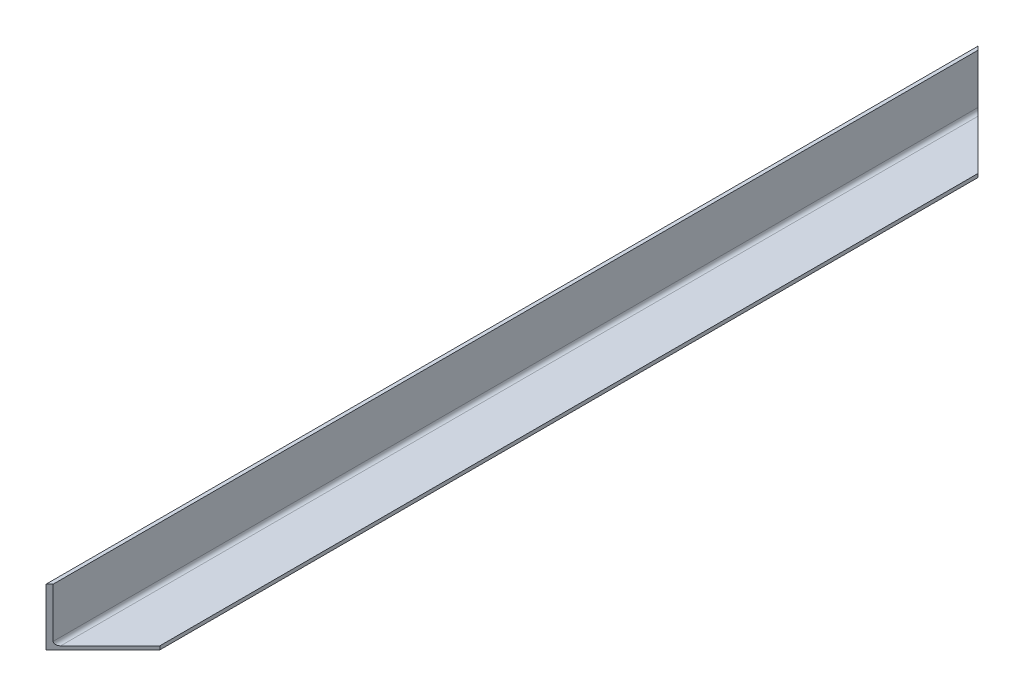
SolidWorks part; units mm, degrees
ref_plane "Front Plane" through (0, 0, 0) normal (0, 0, 1) x (1, 0, 0)
ref_plane "Top Plane" through (0, 0, 0) normal (0, 1, 0) x (1, 0, 0)
ref_plane "Right Plane" through (0, 0, 0) normal (1, 0, 0) x (0, 0, -1)
sketch "Sketch1" plane through (0, 0, 0) normal (0, 0, 1) x (1, 0, 0)
  line L0 (0, -25.4) -> (0, 25.4) construction
  line L1 (25.4, 0) -> (-25.4, 0) construction
  line L2 (-25.4, 25.4) -> (-25.4, -25.4) construction
  line L3 (-25.4, -25.4) -> (25.4, -25.4) construction
  line L4 (25.4, -25.4) -> (25.4, -22.225) construction
  line L5 (25.4, -22.225) -> (-22.225, -22.225) construction
  line L6 (-22.225, -22.225) -> (-22.225, 25.4) construction
  line L7 (-22.225, 25.4) -> (-25.4, 25.4) construction
  line L8 (-22.225, -22.225) -> (-25.4, -22.225) construction
  line L9 (-22.225, -22.225) -> (-22.225, -25.4) construction
  point P4 (0, 0)
  point P8 (0, 0)
  dimension "Wall Thickness" = 3.175
  dimension "Outside Height" = 50.8
  dimension "Outside Width" = 50.8
  dimension "Inside Width" = 47.625
  dimension "Inside Height" = 47.625
sketch "Sketch2" plane through (0, 0, 0) normal (1, 0, 0) x (0, 0, -1)
  line L0 (415.925, 0) -> (-415.925, 0) construction
  line L1 (415.925, -25.4) -> (-415.925, -25.4) construction
  point P0 (-352.425, 0)
  point P4 (0, 0)
  point P5 (352.425, 0)
  point P9 (0, -25.4)
  dimension "Length" = 831.85
  dimension "D1" = 63.5
  dimension "D2" = 63.5
sketch "Sketch4" plane through (0, 0, 0) normal (0, 0, 1) x (1, 0, 0)
  line L0 (-22.225, -22.225) -> (-22.225, 25.4) construction
  line L1 (25.4, -22.225) -> (-22.225, -22.225) construction
  line L2 (25.4, -25.4) -> (25.4, -22.225) construction
  line L3 (-25.4, -25.4) -> (25.4, -25.4) construction
  line L4 (-25.4, 25.4) -> (-25.4, -25.4) construction
  line L5 (-22.225, 25.4) -> (-25.4, 25.4) construction
  line L6 (-22.225, -18.8383) -> (-22.225, 25.4)
  line L7 (25.4, -22.225) -> (-18.8383, -22.225)
  line L8 (25.4, -25.4) -> (25.4, -22.225)
  line L9 (-25.4, -25.4) -> (25.4, -25.4)
  line L10 (-25.4, 25.4) -> (-25.4, -25.4)
  line L11 (-22.225, 25.4) -> (-25.4, 25.4)
  arc A0 (-22.225, -18.8383) -> (-18.8383, -22.225) centre (-18.8383, -18.8383) ccw
  dimension "D1" = 3.3867
extrude "Boss-Extrude1" add sketch "Sketch4" against normal up to vertex (415.925 mm away) and the other way up to vertex (415.925 mm away) up to point (0, 0, -415.925) other way up to point (0, 0, 415.925)
sketch "Sketch5" plane through (0, -22.225, 0) normal (0, 1, 0) x (1, 0, 0)
  line L10 (-25.4, 415.925) -> (25.4, 365.125)
  line L11 (25.4, 415.925) -> (25.4, -415.925) construction
  line L13 (-27.94, 0) -> (27.94, 0) construction
  line L14 (-25.4, 415.925) -> (25.4, 415.925)
  line L15 (25.4, 415.925) -> (25.4, 365.125)
  line L16 (25.4, -415.925) -> (25.4, -365.125)
  line L17 (-25.4, -415.925) -> (25.4, -415.925)
  line L18 (-25.4, -415.925) -> (25.4, -365.125)
  dimension "D1" = 50.8
extrude "Cut-Extrude2" cut sketch "Sketch5" against normal through all both and the other way through all
equation "\"D1@Sketch2\"=\"Outside Height@Sketch1\"*1.25"
equation "\"D2@Sketch2\"=\"D1@Sketch2\""
equation "\"D1@Sketch4\"=\"Outside Height@Sketch1\"/15"
